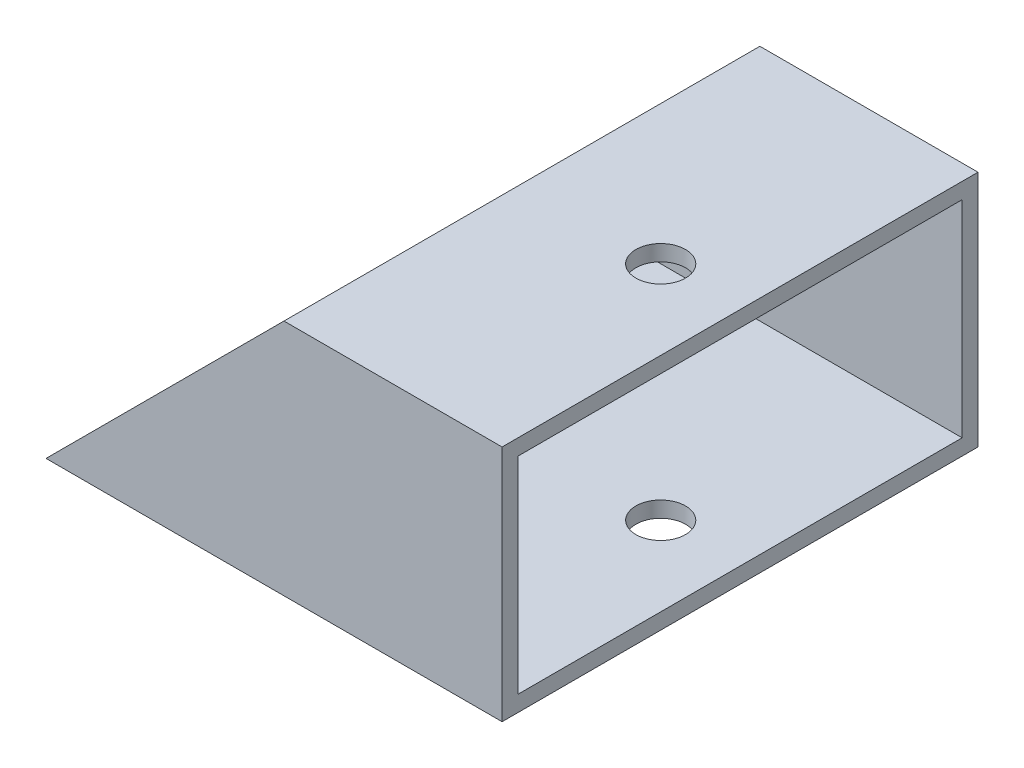
SolidWorks part; units mm, degrees
material "6061-T6 (SS)"
ref_plane "Front Plane" through (0, 0, 0) normal (0, 0, 1) x (1, 0, 0)
ref_plane "Top Plane" through (0, 0, 0) normal (0, 1, 0) x (1, 0, 0)
ref_plane "Right Plane" through (0, 0, 0) normal (1, 0, 0) x (0, 0, -1)
sketch "Sketch1" plane through (0, 0, 0) normal (1, 0, 0) x (0, 0, -1)
  line L1 (-38.1, 19.05) -> (38.1, 19.05)
  line L2 (-38.1, 19.05) -> (-38.1, -19.05)
  line L3 (-38.1, -19.05) -> (38.1, -19.05)
  line L4 (38.1, 19.05) -> (38.1, -19.05)
  line L5 (-38.1, 19.05) -> (38.1, -19.05) construction
  line L6 (-38.1, -19.05) -> (38.1, 19.05) construction
  point P0 (0, 0)
  dimension "D1" = 76.2
  dimension "D2" = 38.1
extrude "Extrude-Thin1" add sketch "Sketch1" along normal blind 101.6 thin
sketch "Sketch2" plane through (0, 0, 38.1) normal (0, 0, 1) x (1, 0, 0)
  line L0 (0, -19.05) -> (38.1, 19.05)
  line L1 (101.6, 19.05) -> (0, 19.05) construction
  line L2 (38.1, 19.05) -> (0, 19.05)
  line L3 (0, 19.05) -> (0, -19.05)
  dimension "D1" = 38.1
extrude "Cut-Extrude1" [suppressed] cut sketch "Sketch2" against normal through all
sketch "Sketch3" [suppressed] plane through (0, -12.7, 0) normal (0, -1, 0) x (-1, 0, 0)
  line L0 (-12.7, 0) -> (0, 0) construction
  line L1 (0, -12.7) -> (0, 12.7) construction
  circle A0 centre (-12.7, 0) radius 1.5875
  circle A1 centre (-25.4, 0) radius 1.5875
  dimension "D1" = 12.7
  dimension "D2" = 3.175
  dimension "D3" = 2
extrude "Cut-Extrude2" [suppressed] cut sketch "Sketch3" against normal through all
sketch "Sketch4" plane through (0, 0, -38.1) normal (0, 0, -1) x (-1, 0, 0)
  line L0 (-101.6, -19.05) -> (0, -19.05) construction
  line L1 (-101.6, -19.05) -> (-101.6, 19.05) construction
  circle A0 centre (-88.9, -6.35) radius 3.9751
  dimension "D1" = 7.9502
  dimension "D2" = 12.7
  dimension "D3" = 12.7
extrude "Cut-Extrude3" [suppressed] cut sketch "Sketch4" against normal through all and the other way through all
sketch "Sketch5" [suppressed] plane through (0, -12.7, 0) normal (0, -1, 0) x (1, 0, 0)
  line L0 (101.6, -12.7) -> (0, -12.7) construction
  line L1 (0, 12.7) -> (50.8, 12.7)
  line L2 (0, 12.7) -> (0, -12.7)
  line L3 (0, -12.7) -> (50.8, -12.7)
  line L4 (50.8, 12.7) -> (50.8, -12.7)
  dimension "D1" = 50.8
extrude "Cut-Extrude4" [suppressed] cut sketch "Sketch5" against normal through all
sketch "Sketch6" [suppressed] plane through (0, 0, -12.7) normal (0, 0, -1) x (-1, 0, 0)
  line L0 (-50.8, 0) -> (-101.6, 0) construction
  line L1 (-50.8, 12.7) -> (-50.8, -12.7) construction
  line L2 (-101.6, -12.7) -> (-101.6, 12.7) construction
  circle A0 centre (-63.5, 0) radius 1.5875
  dimension "D2" = 12.7
  dimension "D1" = 3.175
extrude "Cut-Extrude5" [suppressed] cut sketch "Sketch6" against normal through all
sketch "Sketch7" plane through (0, 19.05, 0) normal (0, 1, 0) x (1, 0, 0)
  line L0 (88.9, 0) -> (0, 0) construction
  line L1 (101.6, 38.1) -> (101.6, -38.1) construction
  circle A0 centre (88.9, 0) radius 3.9751
  dimension "D1" = 7.9502
  dimension "D2" = 12.7
extrude "Cut-Extrude6" cut sketch "Sketch7" against normal through all
sketch "Sketch10" plane through (0, 0, 0) normal (-1, 0, 0) x (0, 0, 1)
  line L4 (-38.1, 19.05) -> (-38.1, -19.05)
  line L5 (-38.1, -19.05) -> (38.1, -19.05)
  line L6 (38.1, -19.05) -> (38.1, 19.05)
  line L7 (38.1, 19.05) -> (-38.1, 19.05)
  line L8 (-38.1, 19.05) -> (-38.1, -19.05)
  line L9 (-38.1, -19.05) -> (38.1, -19.05)
  line L10 (38.1, -19.05) -> (38.1, 19.05)
  line L11 (38.1, 19.05) -> (-38.1, 19.05)
  dimension "D1" = 0
extrude "Cut-Extrude9" cut sketch "Sketch10" against normal blind 28.575
sketch "Sketch11" plane through (0, 0, -38.1) normal (0, 0, -1) x (-1, 0, 0)
  line L0 (-28.575, -19.05) -> (-66.675, 19.05)
  line L1 (-101.6, 19.05) -> (-28.575, 19.05) construction
  line L2 (-66.675, 19.05) -> (-28.575, 19.05)
  line L3 (-28.575, 19.05) -> (-28.575, -19.05)
  dimension "D1" = 45
extrude "Cut-Extrude10" cut sketch "Sketch11" against normal through all
sketch "Sketch9" plane through (0, -16.51, 0) normal (0, 1, 0) x (1, 0, 0)
  line L2 (28.575, 38.1) -> (28.575, -38.1) construction
  line L3 (66.675, -38.1) -> (28.575, -38.1) construction
  circle A0 centre (41.275, 0) radius 1.5875
  circle A1 centre (41.275, -25.4) radius 1.5875
  circle A2 centre (41.275, 25.4) radius 1.5875
  dimension "D3" = 12.7
  dimension "D1" = 3.175
  dimension "D2" = 25.4
  dimension "D4" = 12.7
  dimension "D5" = 25.4
extrude "Cut-Extrude11" cut sketch "Sketch9" against normal through all
equation "\"size1\"= 3in"
equation "\"D1@Sketch1\"= \"size1\""
equation "\"spacing\"= 0.5in"
equation "\"D3@Sketch4\"= \"spacing\""
equation "\"D2@Sketch4\"= \"spacing\""
equation "\"big hole\"=0.313"
equation "\"D1@Sketch4\"= \"big hole\""
equation "\"D2@Sketch6\"= \"spacing\""
equation "\"small hole\"= .125"
equation "\"D1@Sketch6\"= \"small hole\""
equation "\"D2@Sketch7\"=\"spacing\""
equation "\"D1@Sketch7\"=\"big hole\""
equation "\"D1@Sketch9\"=\"small hole\""
equation "\"D3@Sketch9\"=\"spacing\""
equation "\"D4@Sketch9\"=\"spacing\""
equation "\"size2\"= 1.5"
equation "\"D2@Sketch1\"=\"size2\""
